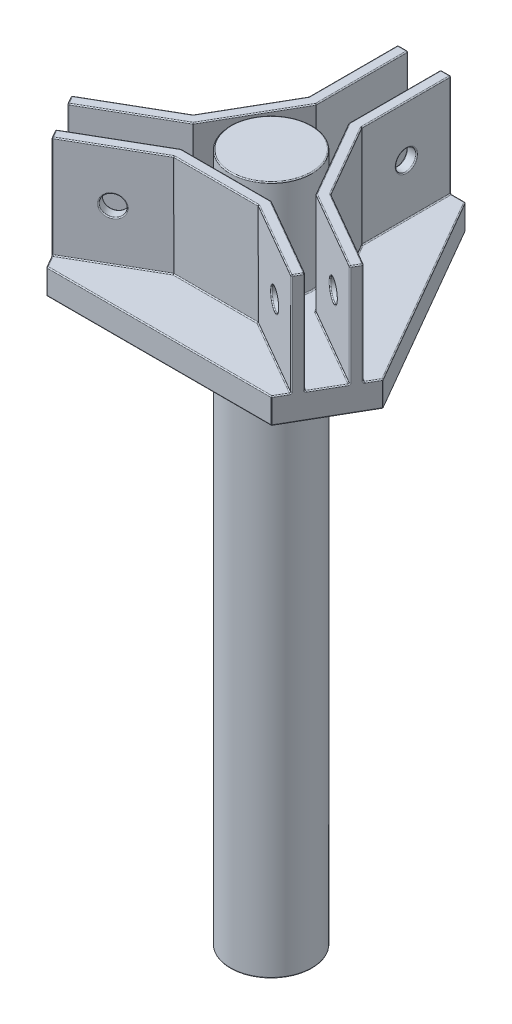
SolidWorks part; units mm, degrees
ref_plane "Front Plane" through (0, 0, 0) normal (0, 0, 1) x (1, 0, 0)
ref_plane "Top Plane" through (0, 0, 0) normal (0, 1, 0) x (1, 0, 0)
ref_plane "Right Plane" through (0, 0, 0) normal (1, 0, 0) x (0, 0, -1)
sketch "Sketch1" plane through (0, 0, 0) normal (0, 1, 0) x (1, 0, 0)
  line L0 (0, 0) -> (-12.999, -7.505) construction
  line L1 (0, 0) -> (0, 15.01) construction
  line L2 (0, 0) -> (12.999, -7.505) construction
  line L3 (-4, 15.01) -> (4, 15.01)
  line L4 (-14.999, -4.0409) -> (-10.999, -10.9691)
  line L5 (10.999, -10.9691) -> (14.999, -4.0409)
  line L9 (-4, 15.01) -> (-14.999, -4.0409)
  line L10 (-10.999, -10.9691) -> (10.999, -10.9691)
  line L11 (14.999, -4.0409) -> (4, 15.01)
  point P8 (0, 15.01)
  point P11 (-12.999, -7.505)
  point P14 (12.999, -7.505)
  dimension "D1" = 120
  dimension "D2" = 120
  dimension "D3" = 8
  dimension "D4" = 8
  dimension "D5" = 8
  dimension "D6" = 15.01
  dimension "D7" = 21.9981
extrude "Boss-Extrude1" add sketch "Sketch1" along normal blind 2.5
sketch "Sketch2" plane through (0, 2.5, 0) normal (0, 1, 0) x (1, 0, 0)
  line L0 (0, 0) -> (0, 15.01) construction
  line L1 (4, 15.01) -> (-4, 15.01) construction
  line L2 (0, 0) -> (-12.999, -7.505) construction
  line L3 (-14.999, -4.0409) -> (-10.999, -10.9691) construction
  line L4 (0, 0) -> (12.999, -7.505) construction
  line L5 (10.999, -10.9691) -> (14.999, -4.0409) construction
  line L6 (-12.199, -8.8906) -> (-4.4048, -4.3906)
  line L7 (-4.4048, -4.3906) -> (4.4048, -4.3906)
  line L8 (4.4048, -4.3906) -> (12.199, -8.8906)
  line L9 (-11.699, -9.7567) -> (-4.1369, -5.3906)
  line L10 (-4.1369, -5.3906) -> (4.1369, -5.3906)
  line L11 (4.1369, -5.3906) -> (11.699, -9.7567)
  line L12 (-12.199, -8.8906) -> (-11.699, -9.7567)
  line L13 (12.199, -8.8906) -> (11.699, -9.7567)
  line L14 (-2.6, 15.01) -> (-2.6, 6.2779)
  line L15 (-1.6, 15.01) -> (-1.6, 6.01)
  line L16 (-1.6, 15.01) -> (-2.6, 15.01)
  line L17 (-1.6, 6.01) -> (-6.0048, -1.6194)
  line L18 (-2.6, 6.2779) -> (-6.7369, -0.8873)
  line L19 (-6.7369, -0.8873) -> (-14.299, -5.2533)
  line L20 (-13.799, -6.1194) -> (-14.299, -5.2533)
  line L21 (-6.0048, -1.6194) -> (-13.799, -6.1194)
  line L22 (14.299, -5.2533) -> (6.7369, -0.8873)
  line L23 (13.799, -6.1194) -> (6.0048, -1.6194)
  line L24 (13.799, -6.1194) -> (14.299, -5.2533)
  line L25 (6.0048, -1.6194) -> (1.6, 6.01)
  line L26 (6.7369, -0.8873) -> (2.6, 6.2779)
  line L27 (2.6, 6.2779) -> (2.6, 15.01)
  line L28 (1.6, 15.01) -> (2.6, 15.01)
  line L29 (1.6, 6.01) -> (1.6, 15.01)
  circle A0 centre (0, 0) radius 4
  point P22 (0, -4.3906)
  point P40 (0, 0)
  dimension "D1" = 8
  dimension "D2" = 9
  dimension "D3" = 1.6
  dimension "D4" = 1
  dimension "D5" = 3
extrude "Boss-Extrude2" add sketch "Sketch2" along normal blind 10
sketch "Sketch3" plane through (0, 0, 0) normal (0, -1, 0) x (1, 0, 0)
  circle A0 centre (0, 0) radius 4 construction
  circle A1 centre (0, 0) radius 4
extrude "Boss-Extrude3" add sketch "Sketch3" along normal blind 55
sketch "Sketch4" plane through (-2.6, 0, 0) normal (-1, 0, 0) x (0, 0, 1)
  line L0 (-6.2779, 7.5) -> (-15.01, 7.5) construction
  line L1 (-6.2779, 12.5) -> (-6.2779, 2.5) construction
  line L2 (-15.01, 12.5) -> (-15.01, 2.5) construction
  circle A0 centre (-10.644, 7.5) radius 1
  dimension "D1" = 2
extrude "Cut-Extrude1" cut sketch "Sketch4" against normal through all and the other way through all
pattern_circular "CirPattern1" count 3 over 360 about axis through (0, 12.5, 0) along (0, -1, 0) of "Cut-Extrude1"
fillet "Fillet1" radius 0.1 106 edges at (9.1519, 7.5, 3.4363) (11.384, 7.5, 3.5703) (9.284, 7.5, 7.2076) (7.0519, 7.5, 7.0737) (-10.884, 7.5, 4.4363) (-9.6519, 7.5, 2.5703) (-7.5519, 7.5, 6.2076) (-8.784, 7.5, 8.0737) (1.6, 7.5, -11.644) (2.6, 7.5, -9.644) (-1.6, 7.5, -9.644) (-2.6, 7.5, -11.644) (0, 0, -4) (10.518, 2.5, 3.0703) (4.6684, 2.5, -2.6953) (2.6, 2.5, -10.644) (1.6, 2.5, -10.51) (3.8024, 2.5, -2.1953) (9.9019, 2.5, 3.8694) (14.049, 12.5, 5.6863) (10.518, 12.5, 3.0703) (4.6684, 12.5, -2.6953) (2.6, 12.5, -10.644) (2.1, 12.5, -15.01) (1.6, 12.5, -10.51) (3.8024, 12.5, -2.1953) (9.9019, 12.5, 3.8694) (13.799, 7.5, 6.1194) (6.0048, 7.5, 1.6194) (1.6, 7.5, -6.01) (1.6, 7.5, -15.01) (2.6, 7.5, -15.01) (2.6, 7.5, -6.2779) (6.7369, 7.5, 0.8873) (14.299, 7.5, 5.2533) (-2.6, 2.5, -10.644) (-4.6684, 2.5, -2.6953) (-10.518, 2.5, 3.0703) (-9.9019, 2.5, 3.8694) (-3.8024, 2.5, -2.1953) (-1.6, 2.5, -10.51) (-2.1, 12.5, -15.01) (-2.6, 12.5, -10.644) (-4.6684, 12.5, -2.6953) (-10.518, 12.5, 3.0703) (-14.049, 12.5, 5.6863) (-9.9019, 12.5, 3.8694) (-3.8024, 12.5, -2.1953) (-1.6, 12.5, -10.51) (-1.6, 7.5, -15.01) (-1.6, 7.5, -6.01) (-6.0048, 7.5, 1.6194) (-13.799, 7.5, 6.1194) (-14.299, 7.5, 5.2533) (-6.7369, 7.5, 0.8873) (-2.6, 7.5, -6.2779) (-2.6, 7.5, -15.01) (-7.918, 2.5, 7.5737) (0, 2.5, 5.3906) (7.918, 2.5, 7.5737) (8.3019, 2.5, 6.6406) (0, 2.5, 4.3906) (-8.3019, 2.5, 6.6406) (-11.949, 12.5, 9.3237) (-7.918, 12.5, 7.5737) (0, 12.5, 5.3906) (7.918, 12.5, 7.5737) (11.949, 12.5, 9.3237) (8.3019, 12.5, 6.6406) (0, 12.5, 4.3906) (-8.3019, 12.5, 6.6406) (-12.199, 7.5, 8.8906) (-4.4048, 7.5, 4.3906) (4.4048, 7.5, 4.3906) (12.199, 7.5, 8.8906) (11.699, 7.5, 9.7567) (4.1369, 7.5, 5.3906) (-4.1369, 7.5, 5.3906) (-11.699, 7.5, 9.7567) (0, 12.5, 4) (9.4995, 0, -5.4846) (0, 0, -15.01) (-9.4995, 0, -5.4846) (-12.999, 0, 7.505) (0, 0, 10.9691) (12.999, 0, 7.505) (9.4995, 2.5, -5.4846) (-3.3, 2.5, -15.01) (0, 2.5, -15.01) (3.3, 2.5, -15.01) (-9.4995, 2.5, -5.4846) (-11.349, 2.5, 10.3629) (-12.999, 2.5, 7.505) (-14.649, 2.5, 4.6471) (0, 2.5, 10.9691) (14.649, 2.5, 4.6471) (12.999, 2.5, 7.505) (11.349, 2.5, 10.3629) (14.999, 1.25, 4.0409) (10.999, 1.25, 10.9691) (-10.999, 1.25, 10.9691) (-14.999, 1.25, 4.0409) (-4, 1.25, -15.01) (4, 1.25, -15.01) (0, 2.5, -4) (0, -55, -4)
